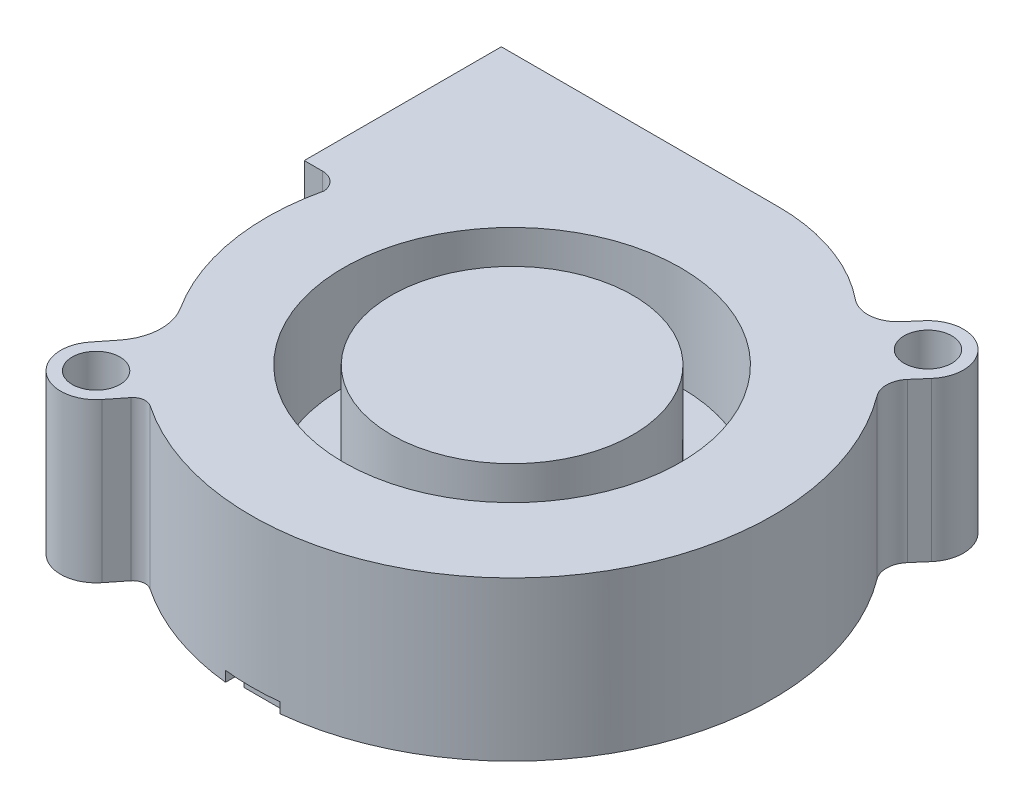
SolidWorks part; units mm, degrees
ref_plane "Front Plane" through (0, 0, 0) normal (0, 0, 1) x (1, 0, 0)
ref_plane "Top Plane" through (0, 0, 0) normal (0, 1, 0) x (1, 0, 0)
ref_plane "Right Plane" through (0, 0, 0) normal (1, 0, 0) x (0, 0, -1)
sketch "Sketch1" plane through (0, 0, 0) normal (0, 1, 0) x (1, 0, 0)
  line L0 (0, 0) -> (0, 19)
  line L1 (0, 0) -> (1.76, 0)
  line L2 (51.5, 11.8013) -> (51.5, -45.6916) construction
  line L3 (6.0874, -23.8939) -> (4.8424, -25.4591)
  line L4 (10.1876, -29.7109) -> (11.4326, -28.1457)
  line L5 (4.1, -32.2) -> (4.1, -48.4773) construction
  line L6 (55.0604, -31) -> (-16.6592, -31) construction
  line L7 (0, 19) -> (26.7, 19)
  line L8 (42.2, 15.2952) -> (43.2694, 16.5254)
  line L9 (48.4241, 12.0446) -> (47.3547, 10.8143)
  line L10 (6.9085, 51.5768) -> (23.5358, 37.5598) construction
  line L12 (19.3543, -32.2) -> (37.3416, -32.2) construction
  line L13 (41.3748, 14.3) -> (31.9305, 14.3) construction
  line L14 (45.8468, 17.7) -> (64.2616, 17.7) construction
  arc A0 (1.76, 0) -> (3.5, -1.5561) centre (1.76, -1.7509) cw
  arc A1 (3.5, -1.5561) -> (6.3729, -18.32) centre (24.7672, -6.5396) ccw
  arc A2 (6.3729, -18.32) -> (6.0874, -23.8939) centre (2.3329, -20.9074) cw
  arc A3 (4.8424, -25.4591) -> (10.1876, -29.7109) centre (7.515, -27.585) ccw
  arc A4 (11.4326, -28.1457) -> (13.0302, -27.8999) centre (12.3644, -28.8868) cw
  arc A5 (26.7, 19) -> (38.2, 14.9411) centre (26.7, 0.6794) cw
  arc A6 (38.2, 14.9411) -> (42.2, 15.2952) centre (40.0163, 17.1935) ccw
  arc A7 (43.2694, 16.5254) -> (48.4241, 12.0446) centre (45.8468, 14.285) cw
  arc A8 (47.3547, 10.8143) -> (47.2487, 7.9792) centre (49.061, 9.331) ccw
  arc A9 (47.2487, 7.9792) -> (13.0302, -27.8999) centre (27.093, -7.0549) cw
  point P42 (47.8894, 11.4294)
  dimension "D5" = 4.1
  dimension "D10" = 21.8433
  dimension "D11" = 1.7509
  dimension "D14" = 6.3729
  dimension "D21" = 4.7
  dimension "D23" = 25.1451
  dimension "D2" = 51.5
  dimension "D3" = 1.76
  dimension "D4" = 3.5
  dimension "D6" = 2
  dimension "D7" = 31
  dimension "D8" = 6.83
  dimension "D9" = 51.5
  dimension "D12" = 26.7
  dimension "D13" = 19
  dimension "D15" = 11.5
  dimension "D16" = 6.83
  dimension "D17" = 1.3
  dimension "D18" = 15.5
  dimension "D19" = 1.2
  dimension "D20" = 49
  dimension "D22" = 1.78
extrude "Boss-Extrude1" add sketch "Sketch1" along normal blind 15.3
sketch "Sketch2" plane through (0, 15.3, 0) normal (0, 1, 0) x (1, 0, 0)
  circle A0 centre (45.8468, 14.285) radius 2.3
  circle A1 centre (7.515, -27.585) radius 2.3
  dimension "D1" = 4.6
extrude "Cut-Extrude1" cut sketch "Sketch2" against normal through all
sketch "Sketch3" plane through (0, 15.3, 0) normal (0, 1, 0) x (1, 0, 0)
  circle A0 centre (27.093, -7.0549) radius 11.65
  circle A1 centre (27.093, -7.0549) radius 16.25
  dimension "D1" = 23.3
  dimension "D2" = 32.5
extrude "Cut-Extrude2" cut sketch "Sketch3" against normal blind 10
sketch "Sketch4" plane through (0, 0, 0) normal (-1, 0, 0) x (0, 0, 1)
  line L8 (-17.7, 1.3) -> (-1.3, 1.3)
  line L9 (-1.3, 1.3) -> (-1.3, 14)
  line L10 (-1.3, 14) -> (-17.7, 14)
  line L11 (-17.7, 14) -> (-17.7, 1.3)
  line L12 (-17.7, 1.3) -> (-1.3, 1.3)
  line L13 (-1.3, 1.3) -> (-1.3, 14)
  line L14 (-1.3, 14) -> (-17.7, 14)
  line L15 (-17.7, 14) -> (-17.7, 1.3)
  dimension "D1" = 1.3
extrude "Cut-Extrude3" cut sketch "Sketch4" against normal blind 5
sketch "Sketch5" plane through (0, 0, 0) normal (0, -1, 0) x (1, 0, 0)
  line L0 (24.473, 32.3) -> (24.473, 22.4)
  line L1 (24.473, 22.4) -> (29.713, 22.4)
  line L2 (29.713, 22.4) -> (29.713, 30.3)
  line L3 (24.473, 32.3) -> (29.713, 32.3)
  line L4 (29.713, 31.6) -> (25.773, 31.6)
  line L5 (25.773, 30.3) -> (29.713, 30.3)
  line L6 (25.773, 31.6) -> (25.773, 30.3)
  line L7 (29.713, 31.6) -> (29.713, 32.3)
  arc A1 (47.2487, -7.9792) -> (13.0302, 27.8999) centre (27.093, 7.0549) ccw construction
  point P8 (27.093, 22.4)
  dimension "D6" = 0.6
  dimension "D1" = 5.24
  dimension "D2" = 9.9
  dimension "D3" = 1.3
  dimension "D4" = 22.4
  dimension "D5" = 1.3
extrude "Cut-Extrude6" cut sketch "Sketch5" against normal blind 1
sketch "Sketch6" plane through (0, 0, 0) normal (0, -1, 0) x (1, 0, 0)
  line L0 (35.8413, 16.1981) -> (43.973, 24.3298)
  line L1 (36.9823, 14.8682) -> (45.1614, 23.0474)
  line L2 (4.7262, 7.1913) -> (16.2429, 7.1913)
  line L3 (50.6929, 8.9413) -> (39.1762, 8.9413)
  line L4 (20.446, 16.9821) -> (11.8626, 24.7359)
  line L5 (19.1758, 15.7751) -> (10.6421, 23.4839)
  line L6 (25.9624, -3.3002) -> (25.9624, -14.8672)
  line L7 (27.7095, -3.4337) -> (27.7095, -14.9337)
  line L8 (18.9827, 0.5769) -> (10.8391, -7.5666)
  line L9 (20.2201, -0.6605) -> (12.0766, -8.8041)
  line L10 (35.199, -0.6605) -> (43.3425, -8.8041)
  line L11 (36.4364, 0.5769) -> (44.5799, -7.5666)
  line L12 (16.2429, 8.9413) -> (4.7262, 8.9413)
  line L13 (39.1762, 7.1913) -> (50.6929, 7.1913)
  line L14 (10.4845, 8.9413) -> (10.4845, 7.1913) construction
  line L15 (14.9089, 19.6295) -> (16.1543, 20.859) construction
  line L16 (39.9071, 20.2639) -> (41.0719, 18.9578) construction
  line L17 (44.9346, 8.9413) -> (44.9346, 7.1913) construction
  line L18 (39.2707, -4.7323) -> (40.5082, -3.4949) construction
  line L19 (27.7095, -9.1837) -> (25.9624, -9.0837) construction
  line L20 (16.1483, -4.7323) -> (14.9109, -3.4949) construction
  line L21 (15.5296, -4.1136) -> (39.8895, 20.2462) construction
  line L22 (15.5316, 20.2443) -> (39.8895, -4.1136) construction
  circle A0 centre (27.7095, 8.0663) radius 11.5
  circle A1 centre (27.7095, 8.0663) radius 23
  point P54 (27.7095, 8.0663)
  line M26 (25.773, 31.6) -> (25.773, 30.3)
  line M27 (25.773, 30.3) -> (29.713, 30.3)
  line M28 (29.713, 30.3) -> (29.713, 22.4)
  line M29 (29.713, 22.4) -> (24.473, 22.4)
  line M30 (24.473, 22.4) -> (24.473, 32.0631)
  dimension "D1" = 23
  dimension "D4" = 46
  dimension "D2" = 27.7095
  dimension "D3" = 8.0663
  dimension "D5" = 1.75
  dimension "D6" = 45
extrude "Cut-Extrude7" cut sketch "Sketch6" against normal blind 0.5 contours L0 A1 L4 A0 M26 M27 M28 M29 M30 | L5 A1 L12 A0 | L2 A1 L8 A0 | L9 A1 L6 A0 | L7 A1 L10 A0 | L11 A1 L13 A0 | L3 A1 L1 A0
sketch "Sketch7" plane through (0, 0, 0) normal (0, -1, 0) x (1, 0, 0)
  line L0 (17.3246, 9.6163) -> (38.0945, 9.6163)
  line L1 (17.3246, 6.5163) -> (38.0945, 6.5163)
  line L2 (27.7095, 9.6163) -> (27.7095, 6.5163) construction
  circle A0 centre (27.7095, 8.0663) radius 10.5
  point P10 (27.7095, 8.0663)
  dimension "D1" = 21
  dimension "D2" = 3.1
split line "Split Line1"
